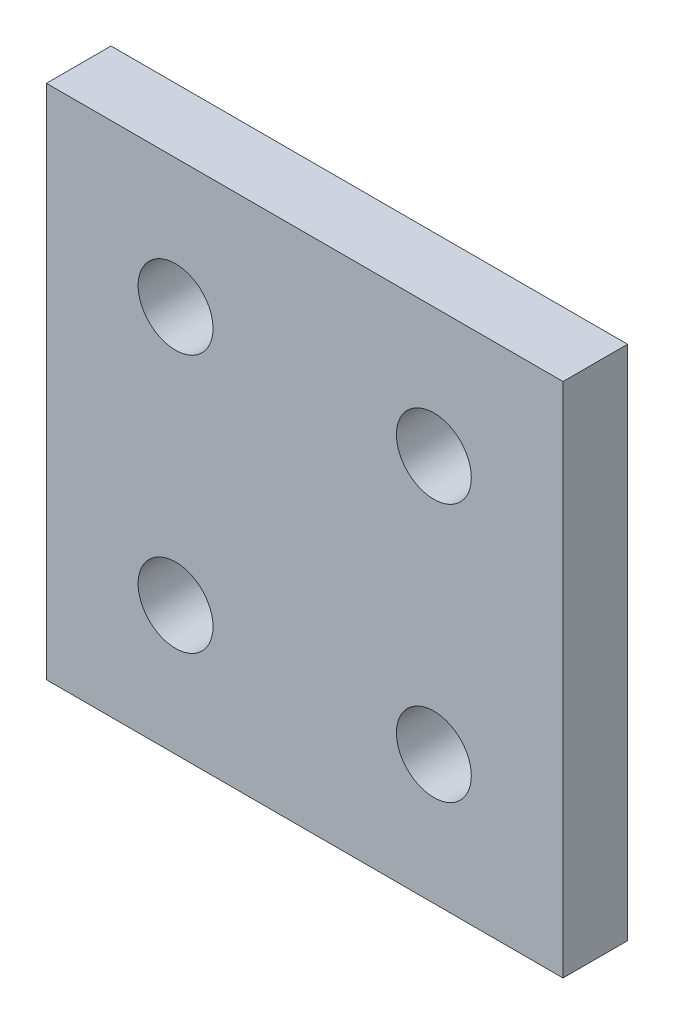
SolidWorks part; units mm, degrees
ref_plane "Front Plane" through (0, 0, 0) normal (0, 0, 1) x (1, 0, 0)
ref_plane "Top Plane" through (0, 0, 0) normal (0, 1, 0) x (1, 0, 0)
ref_plane "Right Plane" through (0, 0, 0) normal (1, 0, 0) x (0, 0, -1)
sketch "Sketch1" plane through (0, 0, 0) normal (0, 0, 1) x (1, 0, 0)
  line L1 (0, 0) -> (40, 0)
  line L2 (0, 0) -> (0, 40)
  line L3 (0, 40) -> (40, 40)
  line L4 (40, 0) -> (40, 40)
  dimension "D1" = 40
  dimension "D2" = 40
extrude "Boss-Extrude1" add sketch "Sketch1" along normal blind 5
hole_wizard "M5 Clearance Hole1" positions "Sketch2" profile "Sketch3" hole size "M5" standard "ANSI Metric" end condition through all
sketch "Sketch2" plane through (0, 0, 5) normal (0, 0, 1) x (1, 0, 0)
  line L0 (40, 40) -> (0, 40) construction
  line L1 (0, 40) -> (0, 0) construction
  point P0 (10, 30)
  point P11 (30, 30)
  point P12 (30, 10)
  point P13 (10, 10)
  dimension "D1" = 10
  dimension "D2" = 10
  dimension "D3" = 2
  dimension "D4" = 2
sketch "Sketch3" plane through (10, 30, 5) normal (1, 0, 0) x (0, -1, 0)
  line L0 (0, 0) -> (0, 5)
  line L1 (0, 5) -> (2.9, 5)
  line L2 (2.9, 5) -> (2.9, 0)
  line L5 (2.9, 0) -> (0, 0)
  line L11 (0, -6.35) -> (0, 107.95) construction
  dimension "Thru Hole Dia." = 5.8
  dimension "Thru Hole Depth" = 5
